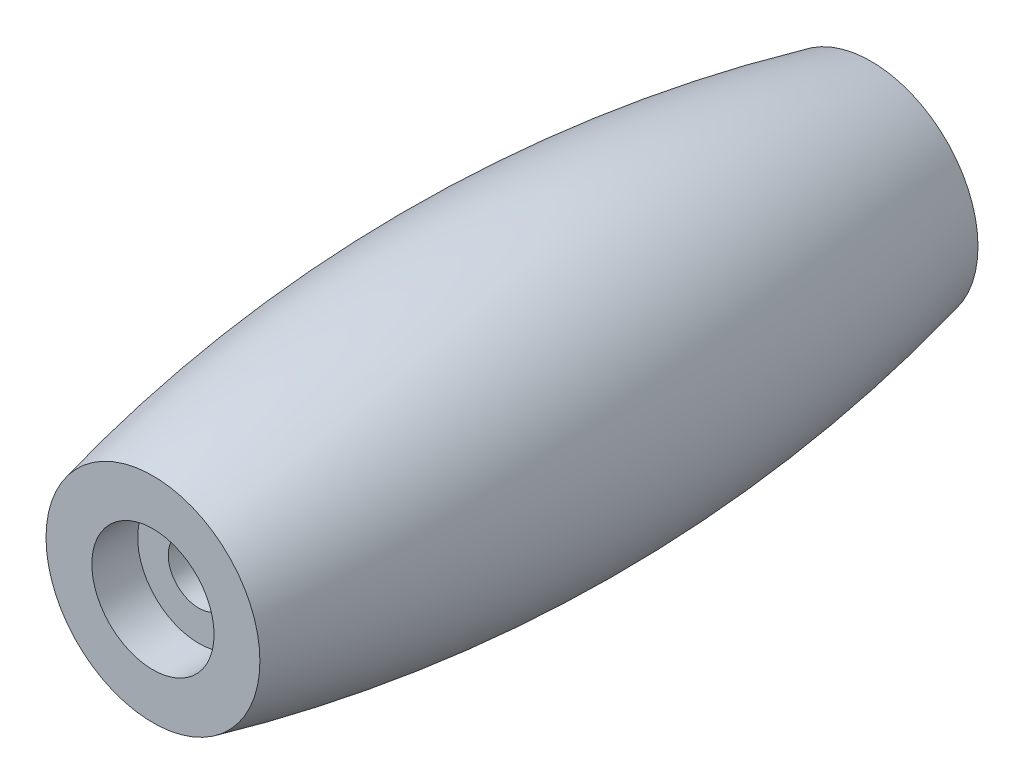
SolidWorks part; units mm, degrees
material "Силиконовая резина"
ref_plane "Спереди" through (0, 0, 0) normal (0, 0, 1) x (1, 0, 0)
ref_plane "Сверху" through (0, 0, 0) normal (0, 1, 0) x (1, 0, 0)
ref_plane "Справа" through (0, 0, 0) normal (1, 0, 0) x (0, 0, -1)
sketch "Эскиз1" plane through (0, 0, 0) normal (0, 1, 0) x (1, 0, 0)
  line L0 (0, 0) -> (0, 47)
  line L1 (0, 47) -> (-7, 47)
  line L3 (-7, 0) -> (0, 0)
  arc A0 (-7, 47) -> (-7, 0) centre (92.9678, 23.5) ccw
  point P4 (-9.725, 23.5)
  point P8 (0, 23.5)
  dimension "D3" = 102.6928
  dimension "D1" = 47
  dimension "D2" = 7
  dimension "D4" = 9.725
revolve "Повернуть1" add sketch "Эскиз1" angle 360 about L0
sketch "Эскиз2" plane through (0, 0, 0) normal (0, 0, 1) x (1, 0, 0)
  circle A0 centre (0, 0) radius 2
  dimension "D1" = 4
extrude "Вырез-Вытянуть1" cut sketch "Эскиз2" against normal through all both and the other way through all
sketch "Эскиз3" plane through (0, 0, 0) normal (0, 0, 1) x (1, 0, 0)
  circle A0 centre (0, 0) radius 4
  dimension "D1" = 8
extrude "Вырез-Вытянуть2" cut sketch "Эскиз3" against normal blind 3
ref_plane "Плоскость1" through (0, 0, -23.5) normal (0, 0, 1) x (1, 0, 0)
mirror "Зеркальное отражение1" about plane through (0, 0, -23.5) normal (0, 0, 1) of "Вырез-Вытянуть2"
